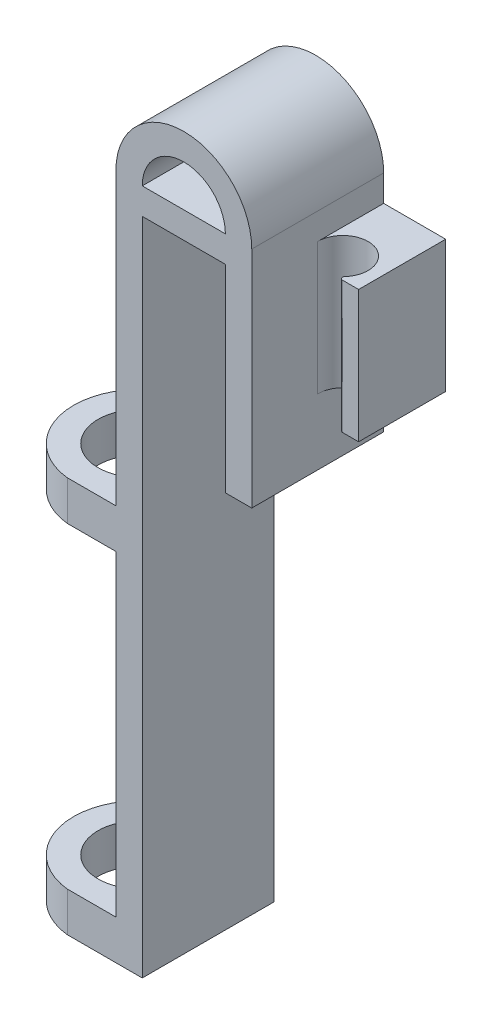
SolidWorks part; units mm, degrees
ref_plane "Front Plane" through (0, 0, 0) normal (0, 0, 1) x (1, 0, 0)
ref_plane "Top Plane" through (0, 0, 0) normal (0, 1, 0) x (1, 0, 0)
ref_plane "Right Plane" through (0, 0, 0) normal (1, 0, 0) x (0, 0, -1)
sketch "Sketch1" plane through (0, 0, 0) normal (0, 0, 1) x (1, 0, 0)
  line L1 (0, 0) -> (-2, 0)
  line L2 (0, 0) -> (0, -50)
  line L3 (0, -50) -> (-2, -50)
  line L4 (-2, 0) -> (-2, -50)
  line L5 (6.3, 0) -> (8.3, 0)
  line L6 (6.3, 0) -> (6.3, -15)
  line L7 (6.3, -15) -> (8.3, -15)
  line L8 (8.3, 0) -> (8.3, -15)
  line L9 (-2, 0) -> (8.3, 0)
  line L10 (-2, 0) -> (-2, 2)
  line L11 (-2, 2) -> (8.3, 2)
  line L12 (8.3, 0) -> (8.3, 2)
  dimension "D1" = 2
  dimension "D2" = 50
  dimension "D3" = 2
  dimension "D4" = 15
  dimension "D5" = 6.3
  dimension "D6" = 2
extrude "Boss-Extrude1" add sketch "Sketch1" along normal blind 10 contours L5 L12 L11 L10 L1 L9 | L8 L5 L6 L7
sketch "Sketch2" plane through (0, 0, 10) normal (0, 0, 1) x (1, 0, 0)
  line L0 (-2, -50) -> (-2, 2) construction
  line L1 (-2, -50) -> (-10.2, -50)
  line L2 (-2, -50) -> (-2, -47)
  line L3 (-2, -47) -> (-10.2, -47)
  line L4 (-10.2, -50) -> (-10.2, -47)
  line L5 (-2, -23) -> (-10.2, -23)
  line L6 (-2, -23) -> (-2, -20)
  line L7 (-2, -20) -> (-10.2, -20)
  line L8 (-10.2, -23) -> (-10.2, -20)
  dimension "D1" = 3
  dimension "D2" = 3
  dimension "D3" = 24
  dimension "D4" = 8.2
extrude "Boss-Extrude2" add sketch "Sketch2" against normal up to surface (10 mm away) up to face at (3.15, -15.75, 0)
sketch "Sketch3" plane through (0, -20, 0) normal (0, 1, 0) x (1, 0, 0)
  line L0 (-10.2, -5) -> (-2, -5) construction
  line L1 (-10.2, 0) -> (-10.2, -10) construction
  line L2 (-2, -10) -> (-2, 0) construction
  circle A0 centre (-5.175, -5) radius 3.175
  point P8 (0, 0)
  dimension "D1" = 6.35
extrude "Cut-Extrude1" cut sketch "Sketch3" against normal up to surface (30 mm away) up to face at (-5.1, -50, 5)
sketch "Sketch4" plane through (0, -20, 0) normal (0, 1, 0) x (1, 0, 0)
  line L0 (-2, 0) -> (-2, -10) construction
  line L1 (-10.2, 0) -> (-10.2, -10) construction
  line L2 (-5.175, 0.025) -> (-10.2, 0)
  line L3 (-10.2, 0) -> (-10.2, -10)
  line L4 (-10.2, -10) -> (-5.175, -10.025)
  arc A1 (-5.175, 0.025) -> (-5.175, -10.025) centre (-5.175, -5) ccw
  line M6 (-2, 0) -> (-10.2, 0)
  line M7 (-10.2, 0) -> (-10.2, -10)
  line M8 (-10.2, -10) -> (-2, -10)
extrude "Cut-Extrude2" cut sketch "Sketch4" against normal up to surface (30 mm away) contours A1 M6 M7 | A1 L3 M8 up to face at (-5.175, -50, 1.825)
sketch "Sketch5" plane through (0, 0, 10) normal (0, 0, 1) x (1, 0, 0)
  line L0 (-2, 2) -> (8.3, 2) construction
  line L1 (-2, 2) -> (0, 2)
  line L2 (6.3, 2) -> (8.3, 2)
  arc A0 (8.3, 2) -> (-2, 2) centre (3.15, 2) ccw
  arc A1 (6.3, 2) -> (0, 2) centre (3.15, 2) ccw
  dimension "D1" = 2
extrude "Boss-Extrude3" add sketch "Sketch5" against normal up to surface (10 mm away) up to face at (-0.1073, -21.8571, 0)
sketch "Sketch6" plane through (0, 0, 10) normal (0, 0, 1) x (1, 0, 0)
  line L0 (8.3, -15) -> (8.3, 2) construction
  line L1 (8.3, 0) -> (13, 0)
  line L2 (8.3, 0) -> (8.3, -10)
  line L3 (8.3, -10) -> (13, -10)
  line L4 (13, 0) -> (13, -10)
  line L5 (0, 0) -> (6.3, 0) construction
  dimension "D1" = 4.7
  dimension "D2" = 10
extrude "Boss-Extrude4" add sketch "Sketch6" against normal up to surface (10 mm away) up to face at (3.15, 3.575, 0)
sketch "Sketch7" plane through (0, 0, 0) normal (0, 1, 0) x (1, 0, 0)
  line L0 (13, -5) -> (8.3, -5) construction
  line L1 (13, 0) -> (13, -10) construction
  line L2 (8.3, 0) -> (8.3, -10) construction
  circle A0 centre (10.21, -5) radius 1.91
  dimension "D1" = 3.82
extrude "Cut-Extrude3" cut sketch "Sketch7" against normal up to surface (10 mm away) up to face at (10.65, -10, 5)
sketch "Sketch8" plane through (0, 0, 0) normal (0, 1, 0) x (1, 0, 0)
  line L0 (13, 0) -> (13, -10) construction
  line L1 (13, -10) -> (8.3, -10) construction
  line L2 (8.3, -5) -> (8.3, -10) construction
  line L3 (13, -6.6) -> (13, -10)
  line L4 (13, -10) -> (8.3, -10)
  line L5 (8.3, -5) -> (8.3, -10)
  line L6 (13, -6.6) -> (11.2531, -6.6)
  circle A0 centre (10.21, -5) radius 1.91 construction
  arc A1 (8.3, -5) -> (11.2531, -6.6) centre (10.21, -5) ccw
  dimension "D1" = 1.6
extrude "Cut-Extrude4" cut sketch "Sketch8" against normal up to surface (10 mm away) up to face at (10.185, -10, 4.6817)
fillet "Fillet1" radius 0.2 1 edges at (11.2531, -5, 6.6)
